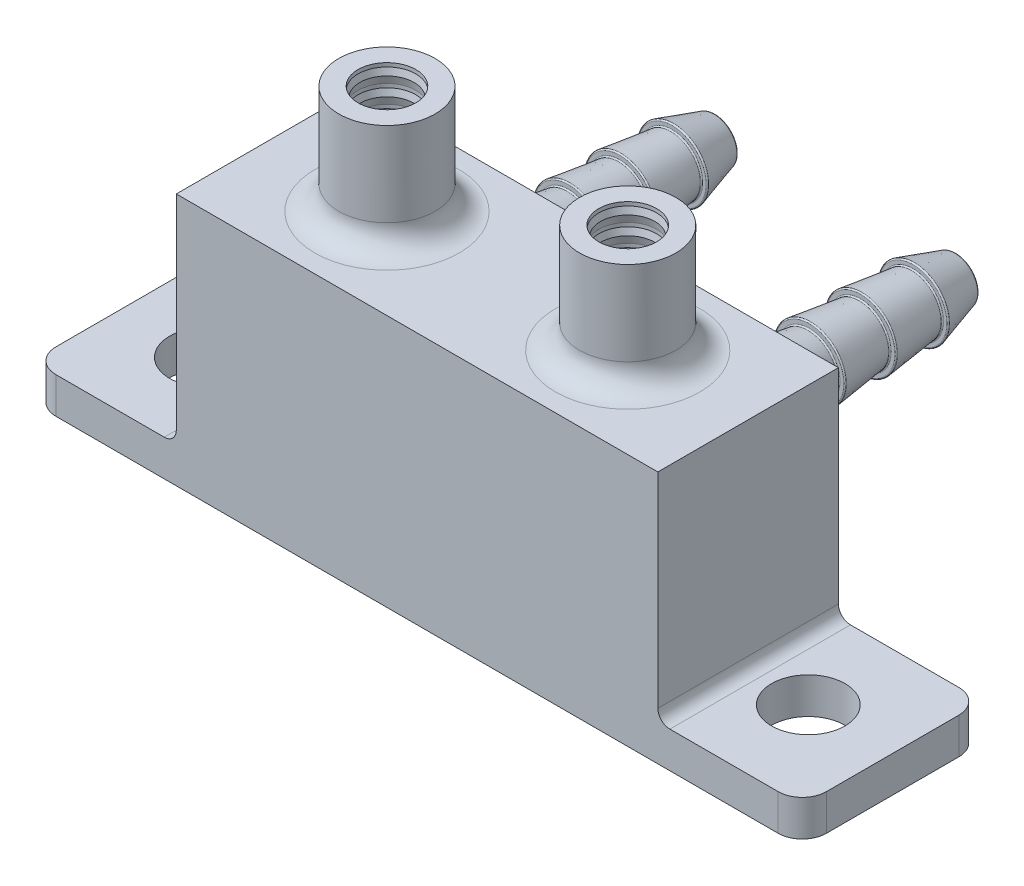
SolidWorks part; units mm, degrees
ref_plane "Front Plane" through (0, 0, 0) normal (0, 0, 1) x (1, 0, 0)
ref_plane "Top Plane" through (0, 0, 0) normal (0, 1, 0) x (1, 0, 0)
ref_plane "Right Plane" through (0, 0, 0) normal (1, 0, 0) x (0, 0, -1)
sketch "Sketch1" plane through (0, 0, 0) normal (0, 1, 0) x (1, 0, 0)
  line L1 (-20, 7.5) -> (20, 7.5)
  line L2 (-20, 7.5) -> (-20, -7.5)
  line L3 (-20, -7.5) -> (20, -7.5)
  line L4 (20, 7.5) -> (20, -7.5)
  dimension "D1" = 40
  dimension "D2" = 15
  dimension "D3" = 20
  dimension "D4" = 7.5
extrude "Boss-Extrude1" add sketch "Sketch1" along normal blind 15
sketch "Sketch2" plane through (0, 15, 0) normal (0, 1, 0) x (1, 0, 0)
  line L1 (-20, 7.5) -> (20, 7.5)
  line L2 (-20, 7.5) -> (-20, -7.5)
  line L3 (-20, -7.5) -> (20, -7.5)
  line L4 (20, 7.5) -> (20, -7.5)
  point P4 (15, -7.5)
  point P5 (-15, -7.5)
extrude "Boss-Extrude2" add sketch "Sketch2" along normal blind 3
sketch "Sketch4" plane through (0, 0, 0) normal (0, 0, 1) x (1, 0, 0)
  line L0 (10, 0) -> (10, 18) construction
  line L2 (12.4, 27) -> (12.4, 26.6871)
  line L3 (12.4, 15) -> (14, 15)
  line L5 (12.4, 27) -> (14, 27)
  line L6 (14, 15) -> (14, 27)
  line L7 (12.4, 15) -> (12.25, 15.6458)
  line L8 (12.25, 15.6458) -> (12.4, 16.1871)
  line L9 (12.25, 17.1458) -> (12.4, 17.6871)
  line L10 (12.4, 16.5) -> (12.25, 17.1458)
  line L11 (12.25, 18.6458) -> (12.4, 19.1871)
  line L12 (12.4, 18) -> (12.25, 18.6458)
  line L13 (12.25, 20.1458) -> (12.4, 20.6871)
  line L14 (12.4, 19.5) -> (12.25, 20.1458)
  line L15 (12.4, 16.5) -> (12.4, 16.1871)
  line L16 (12.4, 18) -> (12.4, 17.6871)
  line L17 (12.4, 19.5) -> (12.4, 19.1871)
  line L18 (12.4, 21) -> (12.25, 21.6458)
  line L19 (12.4, 22.5) -> (12.25, 23.1458)
  line L20 (12.4, 24) -> (12.25, 24.6458)
  line L21 (12.4, 25.5) -> (12.25, 26.1458)
  line L22 (12.25, 21.6458) -> (12.4, 22.1871)
  line L23 (12.25, 23.1458) -> (12.4, 23.6871)
  line L24 (12.25, 24.6458) -> (12.4, 25.1871)
  line L25 (12.25, 26.1458) -> (12.4, 26.6871)
  line L26 (12.4, 21) -> (12.4, 20.6871)
  line L27 (12.4, 22.5) -> (12.4, 22.1871)
  line L28 (12.4, 24) -> (12.4, 23.6871)
  line L29 (12.4, 25.5) -> (12.4, 25.1871)
  line L30 (20, 18) -> (20, 0) construction
  dimension "D1" = 2.4
  dimension "D2" = 4
  dimension "D3" = 12
  dimension "D4" = 2.25
  dimension "D5" = 4
  dimension "D8" = 10
  dimension "D6" = 5
  dimension "D7" = 5
revolve "Revolve1" add sketch "Sketch4" angle 360 about L0
sketch "Sketch5" plane through (0, 0, 0) normal (0, -1, 0) x (1, 0, 0)
  line L0 (0, 0) -> (0, 8.5566) construction
  line L1 (30, -7.5) -> (-30, -7.5)
  line L2 (32, -5.5) -> (32, 5.5)
  line L3 (30, 7.5) -> (-30, 7.5)
  line L4 (-32, -5.5) -> (-32, 5.5)
  circle A0 centre (25, 0) radius 3.05
  circle A1 centre (-25, 0) radius 3.05
  arc A2 (-30, 7.5) -> (-32, 5.5) centre (-30, 5.5) ccw
  arc A3 (-30, -7.5) -> (-32, -5.5) centre (-30, -5.5) cw
  arc A4 (32, 5.5) -> (30, 7.5) centre (30, 5.5) ccw
  arc A5 (30, -7.5) -> (32, -5.5) centre (30, -5.5) ccw
  dimension "D3" = 6.1
  dimension "D4" = 6.1
  dimension "D5" = 2
  dimension "D1" = 32
  dimension "D2" = 32
  dimension "D6" = 25
  dimension "D7" = 50
extrude "Boss-Extrude3" add sketch "Sketch5" along normal blind 3
fillet "Fillet1" radius 2 1 edges at (10, 18, 4)
fillet "Fillet2" radius 1 2 edges at (-20, 0, 0) (20, 0, 0)
ref_plane "Plane1" through (0, 0, 0) normal (0, 0, 1) x (1, 0, 0)
sketch "Sketch9" [suppressed] plane through (0, 0, 0) normal (0, 0, -1) x (-1, 0, 0)
  line L0 (0, 15) -> (0, 10)
  line L1 (2.4, 15) -> (-2.4, 15) construction
  line L2 (-7.5, 8) -> (-2, 8)
  line L3 (-7.5, 15) -> (-7.5, 1) construction
  arc A0 (-2, 8) -> (0, 10) centre (-2, 10) ccw
  dimension "D1" = 2
ref_plane "Plane3" through (10, 0, 0) normal (1, 0, 0) x (0, 0, -1)
sketch "Sketch56" plane through (0, 0, 0) normal (0, 0, 1) x (1, 0, 0)
  line L0 (10, 16) -> (10, 6)
  line L1 (20, 18) -> (20, 1) construction
  arc A0 (10, 6) -> (10, 16) centre (10, 11) ccw
  dimension "D1" = 10
  dimension "D2" = 7
  dimension "D3" = 10
revolve "Cut-Revolve1" cut sketch "Sketch56" angle 360 about L0
sketch "Sketch59" plane through (0, 18, 0) normal (0, 1, 0) x (1, 0, 0)
  line L1 (20, -7.5) -> (20, 7.5) construction
  circle A0 centre (10, 0) radius 2.5
  dimension "D1" = 5
  dimension "D2" = 10
extrude "Cut-Extrude1" cut sketch "Sketch59" against normal up to next
sketch "Sketch60" plane through (0, 0, -7.5) normal (0, 0, -1) x (-1, 0, 0)
  line L0 (-21, 0) -> (-30, 0) construction
  circle A0 centre (0, 8) radius 4
  dimension "D1" = 8
  dimension "D2" = 8
extrude "Cut-Extrude2" [suppressed] cut sketch "Sketch60" against normal up to next
thread "Thread1" [suppressed] pitch 1 start angle 0, offset 0, length 4, pitch 1, diameter 8
ref_plane "Plane2" through (4, 8, -7.5) normal (0, -1, 0) x (1, 0, 0)
sketch "Thread Profile1" plane through (4, 8, -7.5) normal (0, -1, 0) x (1, 0, 0)
  line L0 (0, 0) -> (0, 1) construction
  line L11 (0, 0) -> (0, 0.875)
  line L12 (0, 0.875) -> (-0.5413, 0.5625)
  line L13 (-0.5413, 0.5625) -> (-0.5413, 0.3125)
  line L15 (-0.5413, 0.3125) -> (0, 0)
  line L17 (-0.5413, 0.4375) -> (0, 0.4375) construction
  point P2 (0, 0)
  dimension "Pitch" = 1
  dimension "Profile_Angle" = 60
  dimension "Profile_Land" = 0.25
  dimension "Profile_Height" = 0.5413
chamfer "Chamfer3" [suppressed] distance 0.35 angle 45
fillet "Fillet3" [suppressed] radius 4
sketch "Sketch61" plane through (10, 0, 0) normal (1, 0, 0) x (0, 0, -1)
  line L0 (7.5, 9.5) -> (17.8165, 9.5) construction
  line L2 (7.5, 18) -> (7.5, 1) construction
  line L16 (27.1442, 11.4189) -> (23.812, 12.4224)
  line L17 (7.5, 11) -> (27.0865, 11)
  line L19 (7.5, 12.5) -> (11.4813, 12.5)
  line L20 (27.2865, 11.2) -> (27.2865, 11.2274)
  line L28 (23.6831, 12.3267) -> (23.6831, 12.0531)
  line L29 (23.5709, 11.9539) -> (19.4455, 12.4612)
  line L30 (19.3332, 12.362) -> (19.3332, 12.0538)
  line L31 (19.2205, 11.9546) -> (15.1866, 12.4741)
  line L32 (15.0739, 12.3749) -> (15.0739, 12.0569)
  line L33 (14.9585, 11.958) -> (11.4813, 12.5)
  line L35 (7.5, 12.5) -> (7.5, 11)
  arc A15 (27.0865, 11) -> (27.2865, 11.2) centre (27.0865, 11.2) ccw
  arc A16 (27.1442, 11.4189) -> (27.2865, 11.2274) centre (27.0865, 11.2274) cw
  arc A17 (15.0739, 12.0569) -> (14.9585, 11.958) centre (14.9739, 12.0569) cw
  arc A18 (19.3332, 12.0538) -> (19.2205, 11.9546) centre (19.2332, 12.0538) cw
  arc A19 (23.6831, 12.0531) -> (23.5709, 11.9539) centre (23.5831, 12.0531) cw
  arc A20 (23.812, 12.4224) -> (23.6831, 12.3267) centre (23.7831, 12.3267) ccw
  arc A21 (15.1866, 12.4741) -> (15.0739, 12.3749) centre (15.1739, 12.3749) ccw
  arc A22 (19.4455, 12.4612) -> (19.3332, 12.362) centre (19.4332, 12.362) ccw
  point P32 (27.2865, 11)
  dimension "D3" = 0.1
  dimension "D5" = 0.2
  dimension "D1" = 0.1
  dimension "D2" = 1.5
revolve "Revolve2" add sketch "Sketch61" angle 360 about L0
sketch "Sketch62" plane through (0, 0, -7.5) normal (0, 0, -1) x (-1, 0, 0)
  circle A0 centre (-10, 9.5) radius 1.5
  dimension "D1" = 3
extrude "Cut-Extrude3" cut sketch "Sketch62" against normal up to next
fillet "Fillet5" radius 2 1 edges at (13, 9.5, -7.5)
ref_plane "Plane4" through (0, 0, 0) normal (1, 0, 0) x (0, 0, -1)
mirror "Mirror1" about plane through (0, 0, 0) normal (1, 0, 0) of "Fillet1", "Revolve1", "Fillet5", "Cut-Extrude3", "Revolve2", "Cut-Extrude1", "Cut-Revolve1"
equation "\"D3@Sketch1\"=\"D1@Sketch1\"/2"
equation "\"D4@Sketch1\"=\"D2@Sketch1\"/2"
equation "\"D6@Sketch5\"=\"D7@Sketch5\"/2"
